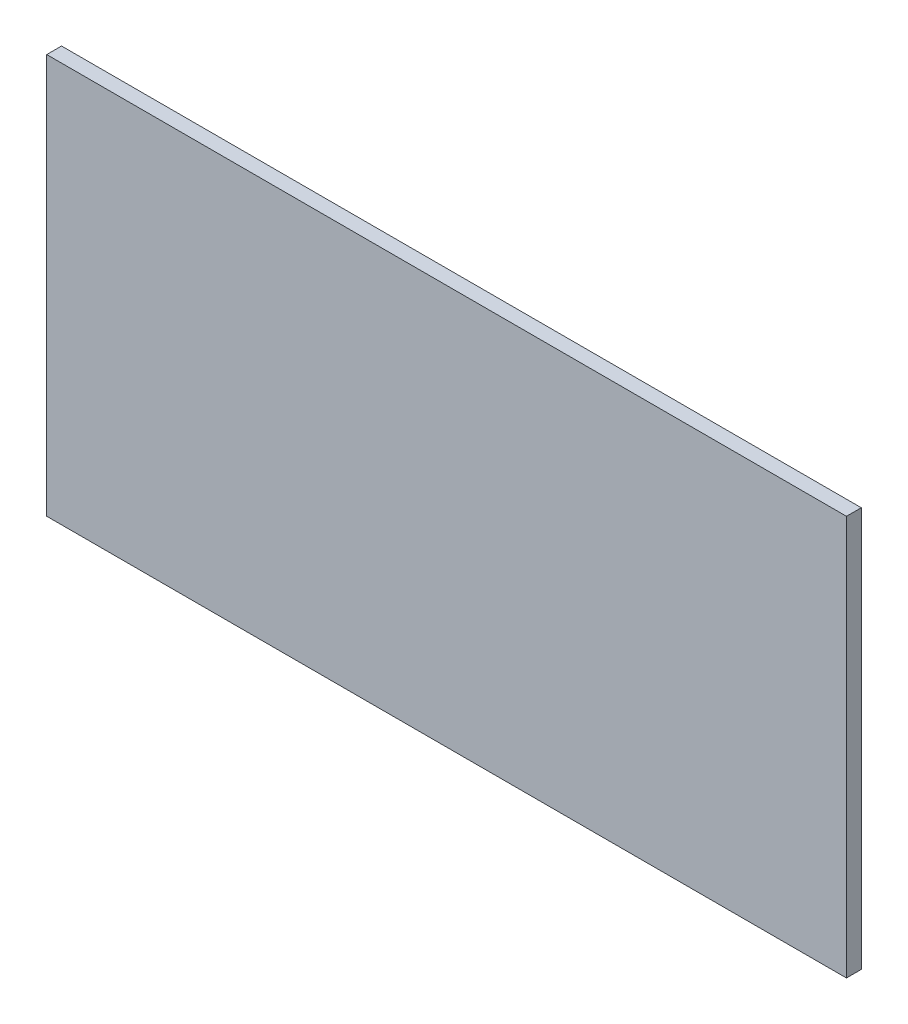
SolidWorks part; units mm, degrees
ref_plane "Front Plane" through (0, 0, 0) normal (0, 0, 1) x (1, 0, 0)
ref_plane "Top Plane" through (0, 0, 0) normal (0, 1, 0) x (1, 0, 0)
ref_plane "Right Plane" through (0, 0, 0) normal (1, 0, 0) x (0, 0, -1)
sketch "Sketch1" plane through (0, 0, 0) normal (0, 0, 1) x (1, 0, 0)
  line L1 (-270, 135) -> (270, 135)
  line L2 (-270, 135) -> (-270, -135)
  line L3 (-270, -135) -> (270, -135)
  line L4 (270, 135) -> (270, -135)
  line L5 (-270, 135) -> (270, -135) construction
  line L6 (-270, -135) -> (270, 135) construction
  point P0 (0, 0)
  dimension "D1" = 540
  dimension "D2" = 270
extrude "Boss-Extrude1" add sketch "Sketch1" along normal blind 10
